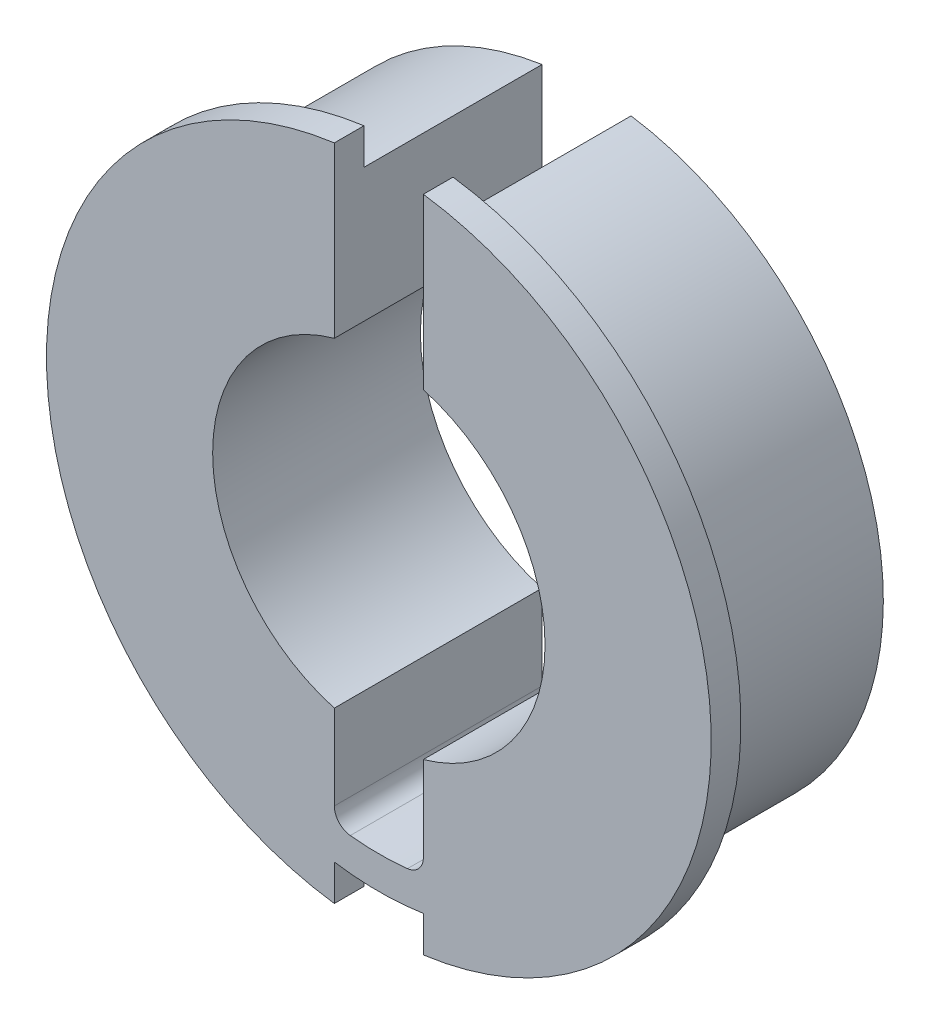
SolidWorks part; units mm, degrees
ref_plane "Front Plane" through (0, 0, 0) normal (0, 0, 1) x (1, 0, 0)
ref_plane "Top Plane" through (0, 0, 0) normal (0, 1, 0) x (1, 0, 0)
ref_plane "Right Plane" through (0, 0, 0) normal (1, 0, 0) x (0, 0, -1)
sketch "Sketch1" plane through (0, 0, 0) normal (0, 0, 1) x (1, 0, 0)
  circle A0 centre (0, 0) radius 12.7
  circle A1 centre (0, 0) radius 7.112
  dimension "D1" = 25.4
  dimension "D2" = 14.224
extrude "Boss-Extrude1" add sketch "Sketch1" along normal blind 7.62
sketch "Sketch2" plane through (0, 0, 7.62) normal (0, 0, 1) x (1, 0, 0)
  circle A0 centre (0, 0) radius 7.112
  circle A3 centre (0, 0) radius 7.112 construction
  circle A4 centre (0, 0) radius 14.224
  circle A5 centre (0, 0) radius 14.224
  dimension "D1" = 1.524
extrude "Boss-Extrude2" add sketch "Sketch2" along normal blind 1.27
sketch "Sketch3" plane through (0, 0, 0) normal (0, 0, -1) x (-1, 0, 0)
  line L0 (0, 0) -> (0, 14.224) construction
  line L1 (-1.905, 14.224) -> (1.905, 14.224)
  line L2 (1.905, 14.224) -> (1.905, -11.1413)
  line L3 (-1.905, 14.224) -> (-1.905, -11.1413)
  line L4 (0, -11.303) -> (0, 0) construction
  circle A0 centre (0, 0) radius 14.224 construction
  arc A3 (-1.905, -11.1413) -> (1.905, -11.1413) centre (0, 0) ccw
  circle A4 centre (0, 0) radius 11.303
  circle A5 centre (0, 0) radius 11.303 construction
  dimension "D1" = 3.81
  dimension "D2" = 1.397
extrude "Cut-Extrude1" cut sketch "Sketch3" against normal through all
sketch "Sketch4" plane through (0, 0, 7.62) normal (0, 0, -1) x (-1, 0, 0)
  line L0 (-1.905, -14.224) -> (-1.905, -12.5563)
  line L1 (1.905, -12.5563) -> (1.905, -14.224)
  line L2 (-1.905, -6.8521) -> (-1.905, -11.1413) construction
  line L3 (1.905, -11.1413) -> (1.905, -6.8521) construction
  line L4 (-1.905, -14.224) -> (1.905, -14.224)
  arc A0 (-1.905, 12.5563) -> (1.905, 12.5563) centre (0, 0) ccw construction
  arc A1 (-1.905, 14.0959) -> (1.905, 14.0959) centre (0, 0) ccw construction
  arc A2 (-1.905, -12.5563) -> (1.905, -12.5563) centre (0, 0) ccw
extrude "Cut-Extrude2" cut sketch "Sketch4" against normal through all
fillet "Fillet1" radius 0.762 2 edges at (-1.905, -11.1413, 4.445) (1.905, -11.1413, 4.445)
